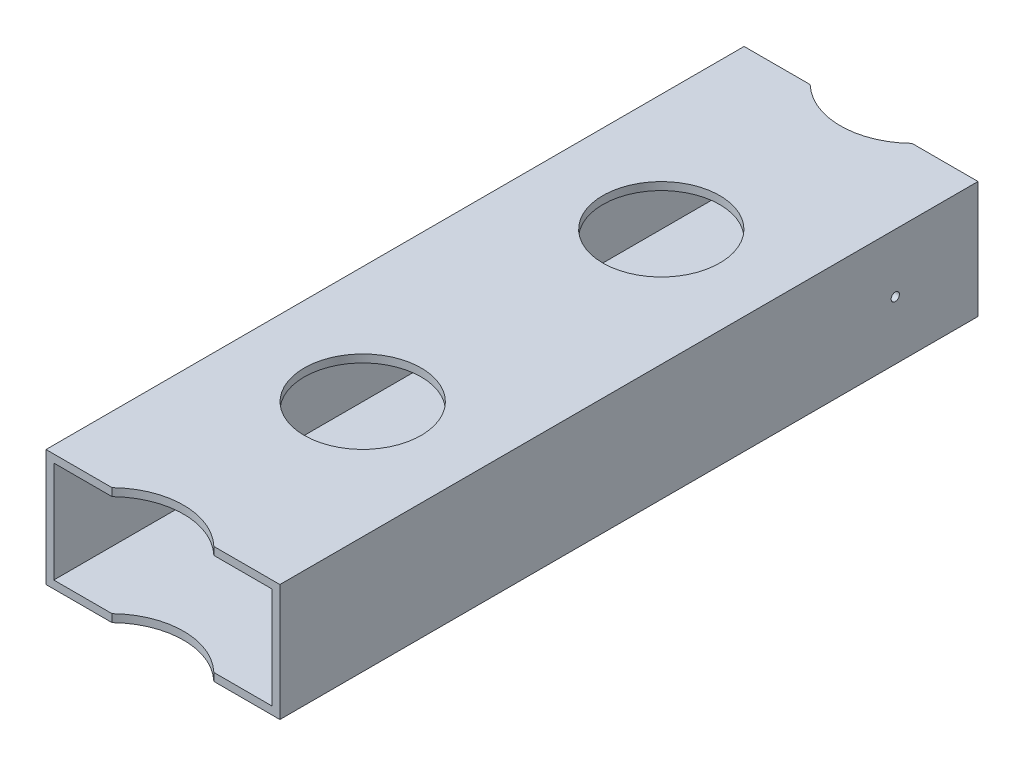
SolidWorks part; units mm, degrees
ref_plane "Front" through (0, 0, 0) normal (0, 0, 1) x (1, 0, 0)
ref_plane "Top" through (0, 0, 0) normal (0, 1, 0) x (1, 0, 0)
ref_plane "Right" through (0, 0, 0) normal (1, 0, 0) x (0, 0, -1)
sketch "Sketch1" plane through (0, 0, 0) normal (0, 0, 1) x (1, 0, 0)
  line L1 (-38.1, -19.05) -> (38.1, -19.05)
  line L2 (-38.1, -19.05) -> (-38.1, 19.05)
  line L3 (-38.1, 19.05) -> (38.1, 19.05)
  line L4 (38.1, -19.05) -> (38.1, 19.05)
  line L5 (-38.1, -19.05) -> (38.1, 19.05) construction
  line L6 (-38.1, 19.05) -> (38.1, -19.05) construction
  point P0 (0, 0)
  dimension "D1" = 38.1
  dimension "D2" = 76.2
extrude "Extrude-Thin1" add sketch "Sketch1" along normal blind 261.62 thin thin type one direction reverse wall 2.54
sketch "Sketch2" plane through (38.1, 0, 0) normal (1, 0, 0) x (0, 0, -1)
  line L0 (-261.62, 0) -> (0, 0) construction
  line L1 (-261.62, -19.05) -> (-261.62, 19.05) construction
  line L2 (0, -19.05) -> (0, 19.05) construction
  circle A0 centre (-252.095, 0) radius 1.3462
  point P8 (-252.095, 0)
  dimension "D1" = 2.6924
  dimension "D2" = 9.525
sketch "Sketch3" plane through (0, 19.05, 0) normal (0, 1, 0) x (1, 0, 0)
  line L0 (38.1, -261.62) -> (-38.1, -261.62) construction
  line L1 (38.1, -17.0861) -> (16.5861, -17.0861)
  line L2 (38.1, -261.62) -> (38.1, 0) construction
  line L3 (-16.5861, -17.0861) -> (-38.1, -17.0861)
  line L4 (-38.1, -261.62) -> (-38.1, 0) construction
  line L6 (38.1, -244.5339) -> (16.5861, -244.5339)
  line L7 (-16.5861, -244.5339) -> (-38.1, -244.5339)
  circle A0 centre (0, 0) radius 23.8125
  circle A1 centre (0, -261.62) radius 23.8125
  point P15 (-38.1, -251.2758)
  point P16 (38.1, -253.313)
  line M3 (38.1, 0) -> (-38.1, 0)
  line M4 (-38.1, 0) -> (-38.1, -261.62)
  line M5 (-38.1, -261.62) -> (38.1, -261.62)
  line M6 (38.1, -261.62) -> (38.1, 0)
  dimension "D1" = 47.625
  dimension "D2" = 17.0861
  dimension "D3" = 17.0861
extrude "Cut-Extrude2" cut sketch "Sketch3" against normal through all contours A1 M5 | A1 L6 M5 M6 | A1 L7 M4 M5 | A0 M3 | A0 L3 M3 M4 | A0 L1 M6 M3
sketch "Sketch4" plane through (0, 19.05, 0) normal (0, 1, 0) x (1, 0, 0)
  line L0 (0, -23.8125) -> (0, -237.8075) construction
  circle A0 centre (0, -179.4464) radius 19.05
  circle A1 centre (0, -82.1736) radius 19.05
  arc A4 (16.5861, -244.5339) -> (-16.5861, -244.5339) centre (0, -261.62) ccw construction
  arc A5 (-16.5861, -17.0861) -> (16.5861, -17.0861) centre (0, 0) ccw construction
  point P16 (19.05, -82.1736)
  dimension "D1" = 38.1
  dimension "D2" = 65.0875
  dimension "D3" = 65.0875
extrude "Cut-Extrude3" cut sketch "Sketch4" against normal through all
sketch "Sketch5" plane through (38.1, 0, 0) normal (1, 0, 0) x (0, 0, -1)
  line L0 (-217.5752, 0) -> (-244.5339, 0) construction
  line L1 (-17.0861, 0) -> (-44.0448, 0) construction
  line L2 (-17.0861, -19.05) -> (-17.0861, 19.05) construction
  line L3 (-244.5339, -19.05) -> (-244.5339, 19.05) construction
  circle A0 centre (-44.0448, 0) radius 1.3462
  point P3 (-44.0448, 0)
  point P10 (-227.9691, -0.0143)
  point P11 (-244.5339, 0)
extrude "Cut-Extrude6" cut sketch "Sketch5" against normal through all
equation "\"D3@Sketch4\"=\"D2@Sketch4\""
equation "\"D3@Sketch3\"=\"D2@Sketch3\""
